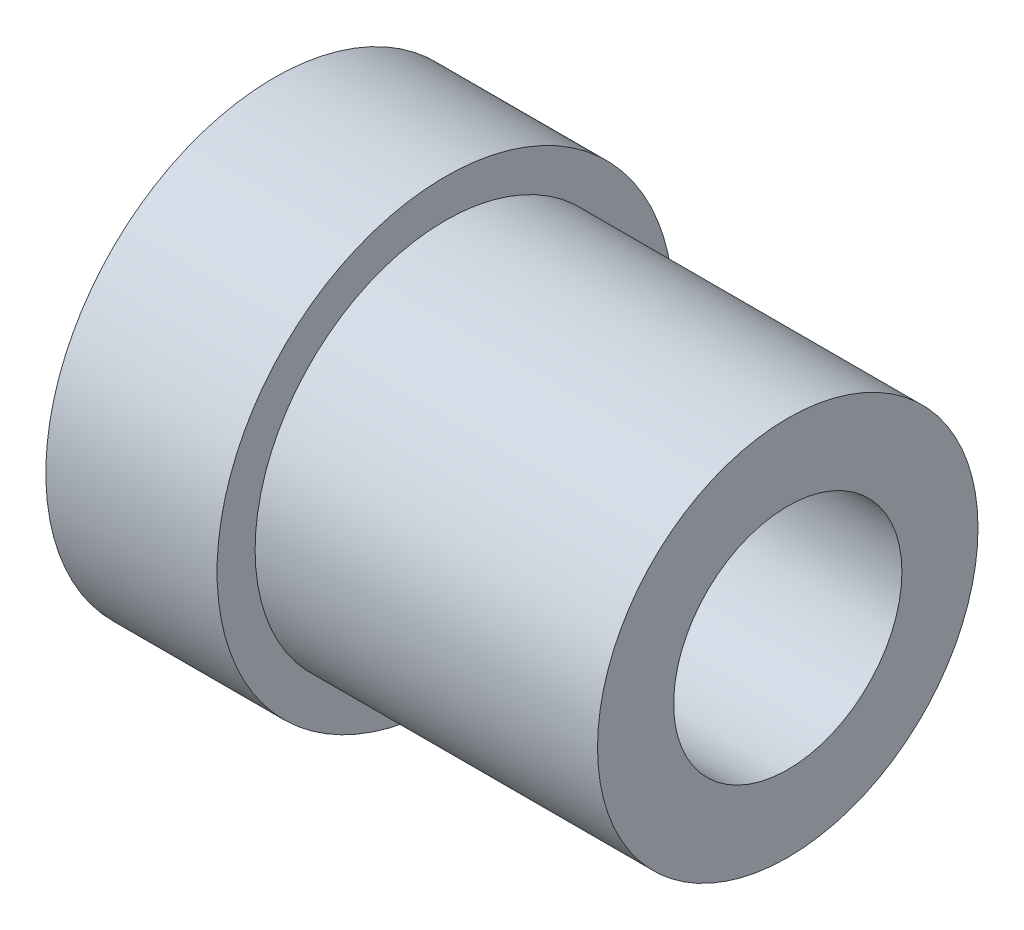
SolidWorks part; units mm, degrees
ref_plane "Front Plane" through (0, 0, 0) normal (0, 0, 1) x (1, 0, 0)
ref_plane "Top Plane" through (0, 0, 0) normal (0, 1, 0) x (1, 0, 0)
ref_plane "Right Plane" through (0, 0, 0) normal (1, 0, 0) x (0, 0, -1)
sketch "Sketch1" plane through (0, 0, 0) normal (1, 0, 0) x (0, 0, -1)
  circle A0 centre (0, 0) radius 3
  circle A1 centre (0, 0) radius 6
extrude "Boss-Extrude1" add sketch "Sketch1" along normal blind 4.5
sketch "Sketch2" plane through (4.5, 0, 0) normal (1, 0, 0) x (0, 0, -1)
  circle A0 centre (0, 0) radius 5
  circle A1 centre (0, 0) radius 3
extrude "Boss-Extrude2" add sketch "Sketch2" along normal blind 9
